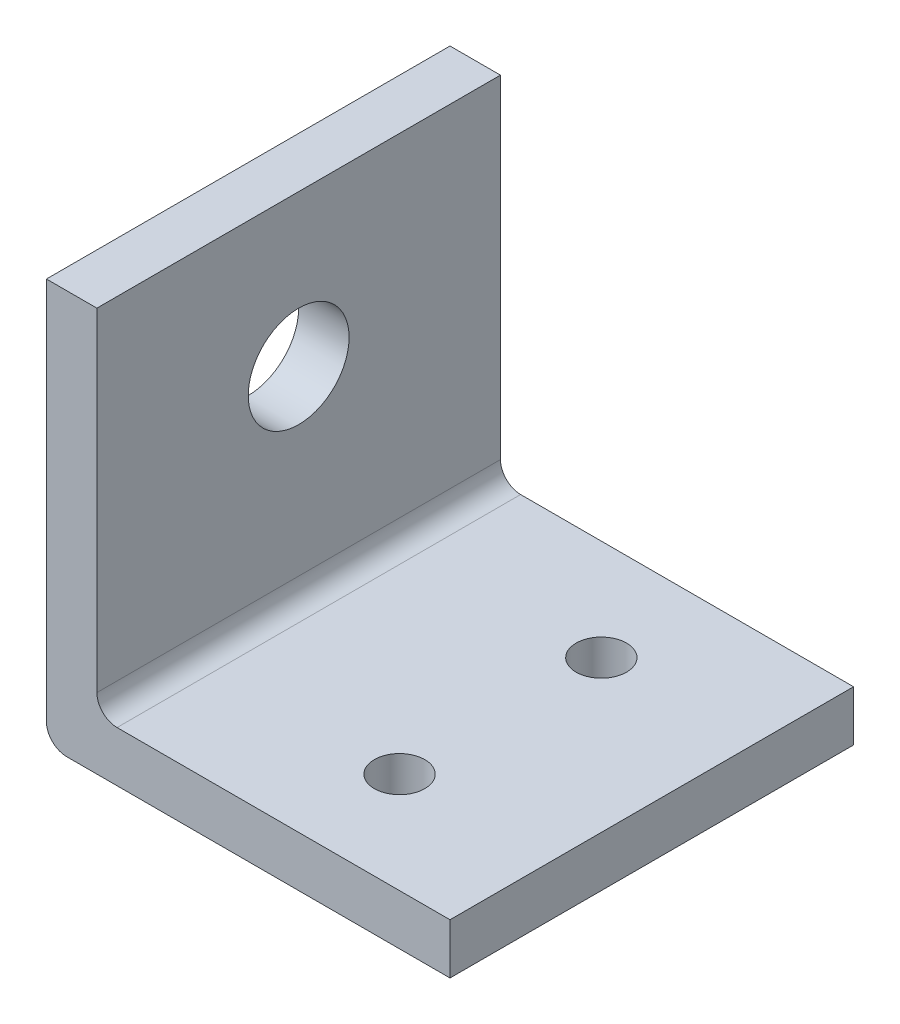
SolidWorks part; units mm, degrees
ref_plane "Front Plane" through (0, 0, 0) normal (0, 0, 1) x (1, 0, 0)
ref_plane "Top Plane" through (0, 0, 0) normal (0, 1, 0) x (1, 0, 0)
ref_plane "Right Plane" through (0, 0, 0) normal (1, 0, 0) x (0, 0, -1)
sketch "Sketch2" plane through (0, 0, 0) normal (0, 0, 1) x (1, 0, 0)
  line L0 (0, 2) -> (0, 40)
  line L1 (2, 0) -> (40, 0)
  line L2 (7, 5) -> (40, 5)
  line L3 (5, 7) -> (5, 40)
  line L4 (5, 5) -> (40, 5) construction
  line L5 (5, 5) -> (5, 40) construction
  line L6 (0, 40) -> (5, 40)
  line L7 (40, 5) -> (40, 0)
  arc A0 (2, 0) -> (0, 2) centre (2, 2) cw
  arc A2 (7, 5) -> (5, 7) centre (7, 7) cw
  arc A3 (5, 5) -> (5, 5) centre (5, 5) cw construction
  point P6 (0, 0)
  dimension "D3" = 2
  dimension "D5" = 2
  dimension "D1" = 40
  dimension "D2" = 40
  dimension "D4" = 5
extrude "Boss-Extrude1" add sketch "Sketch2" along normal blind 40
sketch "Sketch3" plane through (5, 0, 0) normal (1, 0, 0) x (0, 0, -1)
  line L0 (-40, 7) -> (-40, 40) construction
  line L2 (-40, 40) -> (0, 40) construction
  circle A0 centre (-20, 25) radius 5
  point P6 (-19.2005, 16.9815)
  dimension "D1" = 20
  dimension "D2" = 15
extrude "Cut-Extrude1" cut sketch "Sketch3" against normal blind 40
sketch "Sketch4" plane through (0, 5, 0) normal (0, 1, 0) x (1, 0, 0)
  line L0 (40, -40) -> (40, 0) construction
  line L1 (40, -40) -> (7, -40) construction
  circle A0 centre (25, -10) radius 2.5
  circle A1 centre (25, -30) radius 2.5
  dimension "D1" = 15
  dimension "D2" = 15
  dimension "D3" = 10
  dimension "D4" = 20
extrude "Cut-Extrude2" cut sketch "Sketch4" against normal blind 40
